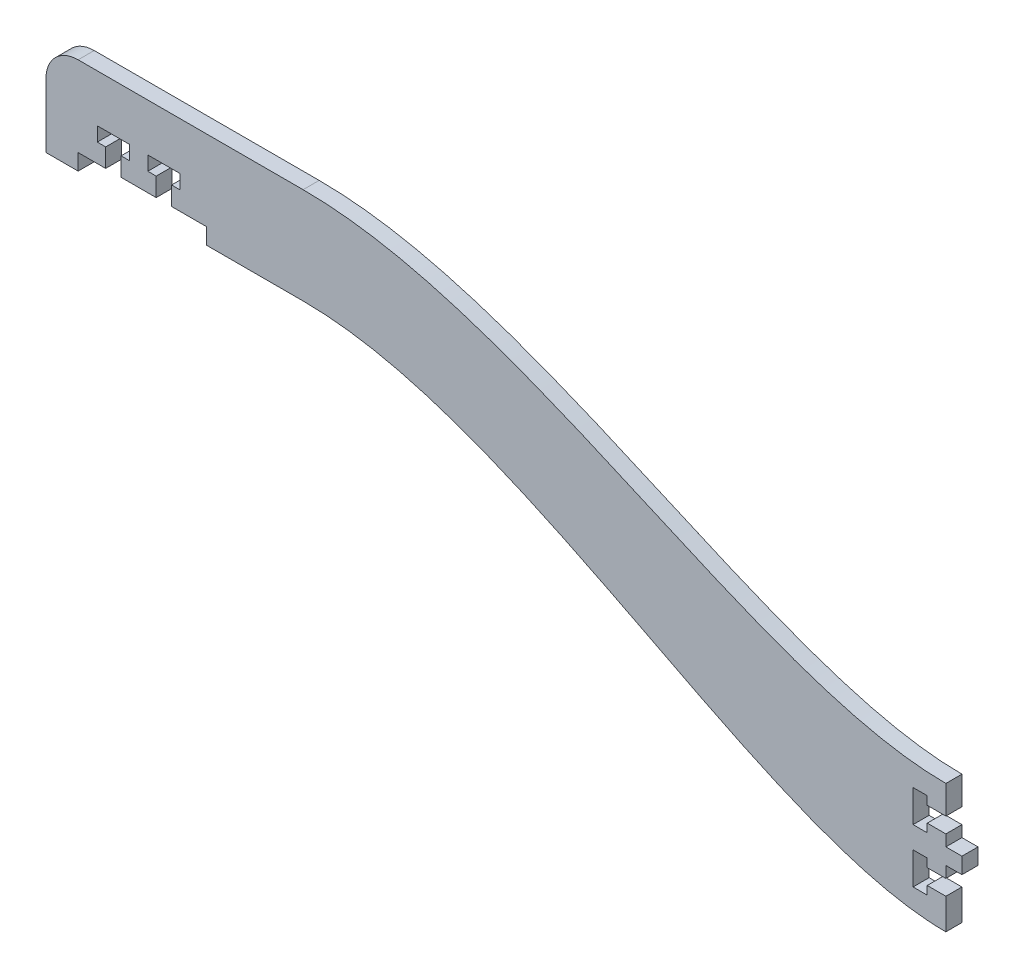
SolidWorks part; units mm, degrees
material "6061 Alloy"
ref_plane "Front Plane" through (0, 0, 0) normal (0, 0, 1) x (1, 0, 0)
ref_plane "Top Plane" through (0, 0, 0) normal (0, 1, 0) x (1, 0, 0)
ref_plane "Right Plane" through (0, 0, 0) normal (1, 0, 0) x (0, 0, -1)
sketch "Sketch1" plane through (0, 0, 0) normal (0, 0, 1) x (1, 0, 0)
  line L0 (-50.8, 12.7) -> (-50.8, 0)
  line L1 (-50.8, 0) -> (-44.45, 0)
  line L2 (-44.45, 0) -> (-44.45, 3.175)
  line L3 (-44.45, 3.175) -> (-39.0144, 3.175)
  line L4 (-39.0144, 3.175) -> (-39.0144, 6.858)
  line L5 (-39.0144, 6.858) -> (-40.6654, 6.858)
  line L6 (-40.6654, 6.858) -> (-40.6654, 9.652)
  line L7 (-40.6654, 9.652) -> (-34.3154, 9.652)
  line L8 (-34.3154, 9.652) -> (-34.3154, 6.858)
  line L9 (-34.3154, 6.858) -> (-35.9664, 6.858)
  line L10 (-35.9664, 6.858) -> (-35.9664, 3.175)
  line L11 (-35.9664, 3.175) -> (-29.0322, 3.175)
  line L12 (-29.0322, 3.175) -> (-29.0322, 6.858)
  line L13 (-29.0322, 6.858) -> (-30.6832, 6.858)
  line L14 (-30.6832, 6.858) -> (-30.6832, 9.652)
  line L15 (-30.6832, 9.652) -> (-24.3332, 9.652)
  line L16 (-24.3332, 9.652) -> (-24.3332, 6.858)
  line L17 (-24.3332, 6.858) -> (-25.9842, 6.858)
  line L18 (-25.9842, 6.858) -> (-25.9842, 3.175)
  line L19 (-25.9842, 3.175) -> (-19.05, 3.175)
  line L20 (-19.05, 3.175) -> (-19.05, 0)
  line L21 (-19.05, 0) -> (0, 0)
  line L22 (-44.45, 19.05) -> (0, 19.05)
  line L23 (127, -19.05) -> (127, -24.638)
  line L24 (52.478, 19.05) -> (-52.5388, 19.05) construction
  line L25 (52.504, 0) -> (-52.5128, 0) construction
  line L26 (127, -24.638) -> (123.317, -24.638)
  line L27 (123.317, -24.638) -> (123.317, -22.987)
  line L28 (123.317, -22.987) -> (120.523, -22.987)
  line L29 (120.523, -22.987) -> (120.523, -29.337)
  line L30 (120.523, -29.337) -> (123.317, -29.337)
  line L31 (123.317, -29.337) -> (123.317, -27.686)
  line L32 (123.317, -27.686) -> (127, -27.686)
  line L33 (127, -27.686) -> (127, -29.9085)
  line L34 (127, -35.306) -> (123.317, -35.306)
  line L35 (123.317, -35.306) -> (123.317, -33.655)
  line L36 (123.317, -33.655) -> (120.523, -33.655)
  line L37 (120.523, -33.655) -> (120.523, -40.005)
  line L38 (120.523, -40.005) -> (123.317, -40.005)
  line L39 (123.317, -40.005) -> (123.317, -38.354)
  line L40 (123.317, -38.354) -> (127, -38.354)
  line L41 (127, -38.354) -> (127, -44.45)
  line L42 (164.6938, -44.45) -> (89.3062, -44.45) construction
  line L43 (156.61, -19.05) -> (97.39, -19.05) construction
  line L44 (127, -29.9085) -> (130.175, -29.9085)
  line L45 (130.175, -29.9085) -> (130.175, -33.0835)
  line L46 (130.175, -33.0835) -> (127, -33.0835)
  line L47 (127, -33.0835) -> (127, -35.306)
  arc A0 (-50.8, 12.7) -> (-44.45, 19.05) centre (-44.45, 12.7) cw
  spline S0 degree 3 poles (0, 19.05) (43.757, 19.05) (89.9875, -19.05) (127, -19.05) knots 0 0 0 0 1 1 1 1
  spline S1 degree 3 poles (0, 0) (43.757, 0) (90.568, -44.45) (127, -44.45) knots 0 0 0 0 1 1 1 1
  point P29 (-50.8, 19.05)
  dimension "D14" = 6.35
  dimension "D1" = 6.35
  dimension "D2" = 3.048
  dimension "D3" = 6.477
  dimension "D4" = 2.794
  dimension "D5" = 6.35
  dimension "D6" = 3.175
  dimension "D7" = 19.05
  dimension "D8" = 6.9342
  dimension "D9" = 6.9342
  dimension "D10" = 25.4
  dimension "D11" = 50.8
  dimension "D12" = 25.4
  dimension "D13" = 6.477
  dimension "D15" = 3.048
  dimension "D16" = 2.794
  dimension "D17" = 177.8
  dimension "D18" = 6.35
  dimension "D19" = 44.45
  dimension "D20" = 5.588
  dimension "D21" = 7.62
  dimension "D22" = 3.175
  dimension "D23" = 2.2225
  dimension "D24" = 3.175
extrude "Boss-Extrude1" add sketch "Sketch1" along normal blind 3.175
